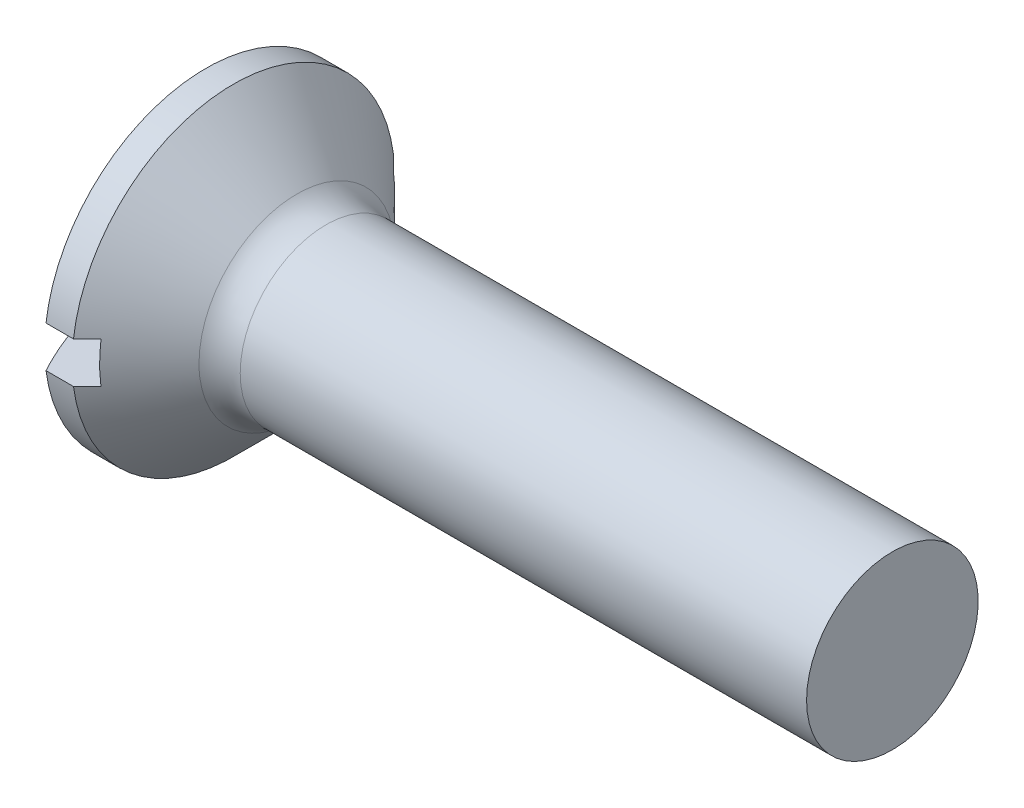
SolidWorks part; units mm, degrees
ref_plane "Plane1" through (0, 0, 0) normal (0, 0, 1) x (1, 0, 0)
ref_plane "Plane2" through (0, 0, 0) normal (0, 1, 0) x (1, 0, 0)
ref_plane "Plane3" through (0, 0, 0) normal (1, 0, 0) x (0, 0, -1)
sketch "BodySke" plane through (0, 0, 0) normal (0, 0, 1) x (1, 0, 0)
  line L0 (0, 0) -> (10.6, 0)
  line L1 (10.6, 0) -> (10.6, 1.25)
  line L2 (10.6, 1.25) -> (2.1, 1.25)
  line L3 (1, -2.35) -> (2.1, -1.25) construction
  line L4 (-15.875, 0) -> (82.55, 0) construction
  line L5 (1, 2.35) -> (2.1, 1.25)
  line L6 (2.55, 4.425) -> (2.55, -11.45) construction
  line L7 (0.6, 2.7793) -> (0.6, -13.0957) construction
  line L8 (1, 2.35) -> (0.6, 2.35)
  arc A0 (0, 0) -> (0.6, 2.35) centre (4.9021, 0) cw
  dimension "Head_ang" = 90
  dimension "Diameter" = 2.5
  dimension "Advance" = 0.45
  dimension "Thread_nom" = 10
  dimension "Oval_ht" = 0.6
  dimension "Side_ht" = 1.5
  dimension "Head_dia" = 4.7
  dimension "Length" = 10
revolve "Base-Revolve" add sketch "BodySke"
cosmetic thread "ThreadCosmetic"
extrude "Slot" cut sketch "Sketch2" along normal blind 1.2
sketch "Sketch2" plane through (0, 0, 0) normal (1, 0, 0) x (0, 0, -1)
  line L0 (2.35, -0.3) -> (-2.35, -0.3)
  line L1 (2.35, -0.3) -> (2.35, 0.3)
  line L2 (-2.35, 0.3) -> (2.35, 0.3)
  line L3 (-2.35, 0.3) -> (-2.35, -0.3)
  dimension "D1" = 4.7
  dimension "Slot_width" = 0.6
  dimension "D3" = 2.35
  dimension "D4" = 0.3
fillet "Fillet1" radius 0.6 1 edges at (2.1, 0, 1.25)
sketch "ThdSchSke" plane through (0, 0, 0) normal (0, 0, 1) x (1, 0, 0)
  line L0 (2.55, -0.9965) -> (2.3725, -1.25)
  line L1 (2.55, -0.9965) -> (2.7275, -1.25)
  line L2 (2.7275, -1.25) -> (2.7275, -1.5625)
  line L3 (-3.175, 0) -> (5.1513, 0) construction
  line L5 (2.7275, -1.5625) -> (2.3725, -1.5625)
  line L6 (2.3725, -1.5625) -> (2.3725, -1.25)
  dimension "Diameter" = 2.5
  dimension "SideAngle" = 55
  dimension "VeeAngle" = 70
  dimension "Thread_minor" = 1.993
  dimension "Overcut" = 3.125
  dimension "Start" = 2.55
revolve "ThreadSchematic" [suppressed] cut sketch "ThdSchSke" angle 360 about L3
pattern_linear "ThdSchPat" [suppressed]
equation "\"D1@Sketch2\" = \"Head_dia@BodySke\""
equation "\"D3@Sketch2\" = \"D1@Sketch2\" / 2"
equation "\"D4@Sketch2\" = \"Slot_width@Sketch2\" / 2"
equation "\"Thread_length@ThreadCosmetic\" = ((sgn( (\"Length@BodySke\" - \"Advance@BodySke\" - \"Side_ht@BodySke\" ) - \"Thread_nom@BodySke\" )-1)*( (\"Length@BodySke\" - \"Advance@BodySke\" - \"Side_ht@BodySke\" ) - \"Thread_nom@BodySke\" ))/-2+ \"Thread_nom@BodySke\""
equation "\"Thread_minor@ThdSchSke\" = \"Thread_minor@ThreadCosmetic\""
equation "\"Diameter@ThdSchSke\" = \"Diameter@BodySke\""
equation "\"Overcut@ThdSchSke\" = \"Diameter@BodySke\" * 1.25"
equation "\"Start@ThdSchSke\" = \"Oval_ht@BodySke\" + \"Length@BodySke\" - \"Thread_length@ThreadCosmetic\"  '---Countersunk---"
equation "\"Num_threads@ThdSchPat\" = int( \"Thread_length@ThreadCosmetic\" / \"Advance@BodySke\" + 0.999 )  + 1"
equation "\"Advance@ThdSchPat\" = \"Thread_length@ThreadCosmetic\" /  (\"Num_threads@ThdSchPat\" - 1) 'relax it"
